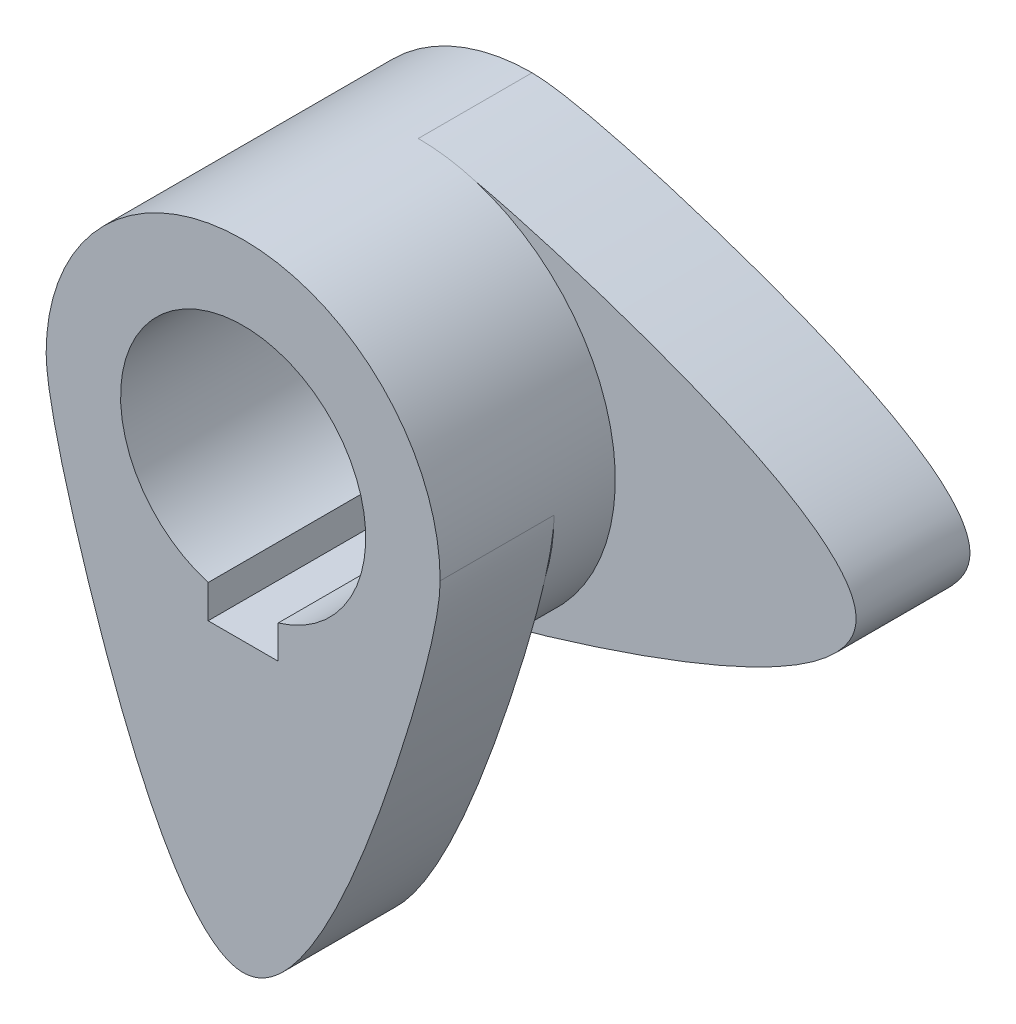
SolidWorks part; units mm, degrees
ref_plane "前视基准面" through (0, 0, 0) normal (0, 0, 1) x (1, 0, 0)
ref_plane "上视基准面" through (0, 0, 0) normal (0, 1, 0) x (1, 0, 0)
ref_plane "右视基准面" through (0, 0, 0) normal (1, 0, 0) x (0, 0, -1)
sketch "草图1" plane through (0, 0, 0) normal (0, 0, 1) x (1, 0, 0)
  line L0 (0, 0) -> (57.7088, 0) construction
  circle A0 centre (0, 0) radius 14
  arc A1 (0, 22.5) -> (0, -22.5) centre (0, 0) ccw
  spline S0 degree 3 poles (0, 22.5) (3.7426, 22.5) (25.152, 16.9441) (65.2957, 0) (25.155, -16.9441) (3.7383, -22.5) (0, -22.5) knots 0 0 0 0 0.192196 0.5 0.807804 1 1 1 1
  point P4 (50, 0)
  dimension "D1" = 28
  dimension "D2" = 45
  dimension "D3" = 50
  dimension "D4" = 35
extrude "凸台-拉伸1" add sketch "草图1" along normal blind 13
sketch "草图2" plane through (0, 0, 13) normal (0, 0, 1) x (1, 0, 0)
  circle A0 centre (0, 0) radius 22.5
  dimension "D1" = 45
extrude "凸台-拉伸2" add sketch "草图2" along normal blind 7
sketch "草图3" plane through (0, 0, 20) normal (0, 0, 1) x (1, 0, 0)
  arc A1 (22.5, 0) -> (-22.5, 0) centre (0, 0) ccw
  spline S0 degree 3 poles (22.5, 0) (22.5, -3.7426) (16.9441, -25.152) (0, -65.2957) (-16.9441, -25.155) (-22.5, -3.7383) (-22.5, 0) knots 0 0 0 0 0.192196 0.5 0.807804 1 1 1 1
  point P3 (0, -50)
  dimension "D4" = 0
extrude "凸台-拉伸3" add sketch "草图3" along normal blind 13
sketch "草图4" plane through (0, 0, 13) normal (0, 0, -1) x (-1, 0, 0)
  circle A0 centre (0, 0) radius 14
extrude "切除-拉伸1" cut sketch "草图4" against normal blind 40
sketch "草图5" plane through (0, 0, 33) normal (0, 0, 1) x (1, 0, 0)
  line L0 (0, 0) -> (0, -34.5001) construction
  line L1 (0, -14) -> (8, -14) construction
  line L2 (-4, -14) -> (-4, -9.1536)
  line L4 (4, -14) -> (4, -17.2)
  line L5 (4, -17.2) -> (-4, -17.2)
  line L6 (-4, -14) -> (-4, -17.2)
  line L7 (-4, -9.1536) -> (4, -9.1536)
  line L8 (4, -9.1536) -> (4, -14)
  circle A1 centre (0, 0) radius 14 construction
  dimension "D1" = 3.2
  dimension "D2" = 8
  dimension "D3" = 4
extrude "切除-拉伸2" cut sketch "草图5" against normal blind 41
